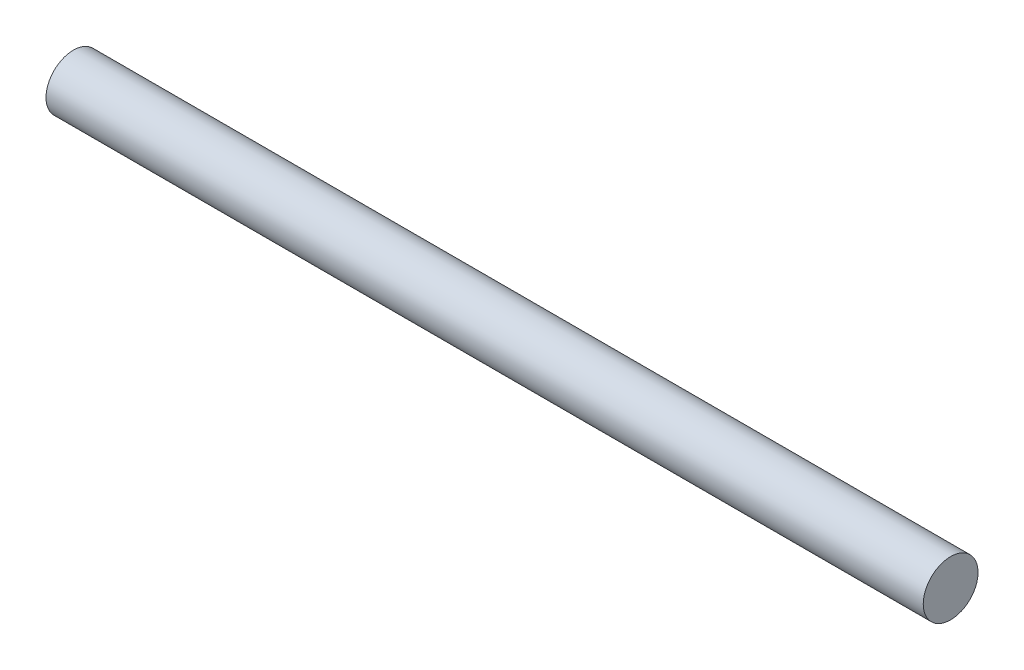
SolidWorks part; units mm, degrees
ref_plane "前视基准面" through (0, 0, 0) normal (0, 0, 1) x (1, 0, 0)
ref_plane "上视基准面" through (0, 0, 0) normal (0, 1, 0) x (1, 0, 0)
ref_plane "右视基准面" through (0, 0, 0) normal (1, 0, 0) x (0, 0, -1)
sketch "草图1" plane through (0, 0, 0) normal (0, 0, 1) x (1, 0, 0)
  line L1 (0, 0) -> (480, 0)
  line L2 (0, 0) -> (0, 15)
  line L3 (0, 15) -> (480, 15)
  line L4 (480, 0) -> (480, 15)
  dimension "D1" = 480
  dimension "D2" = 15
revolve "旋转1" add sketch "草图1" angle 360 about L1
